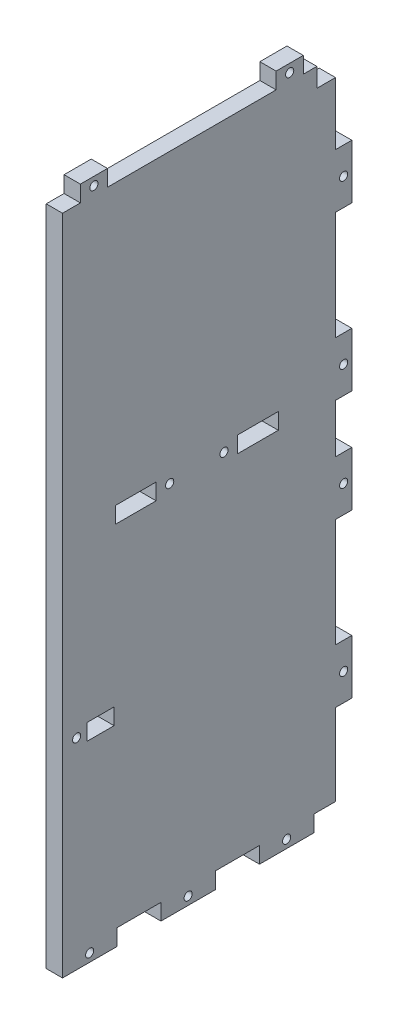
SolidWorks part; units mm, degrees
ref_plane "Plan de face" through (0, 0, 0) normal (0, 0, 1) x (1, 0, 0)
ref_plane "Plan de dessus" through (0, 0, 0) normal (0, 1, 0) x (1, 0, 0)
ref_plane "Plan de droite" through (0, 0, 0) normal (1, 0, 0) x (0, 0, -1)
sketch "Esquisse1" plane through (0, 0, 0) normal (1, 0, 0) x (0, 0, -1)
  line L0 (97.1531, 0) -> (-102.2664, 0) construction
  line L1 (-50.29, 119) -> (50.29, 119)
  line L2 (-50.29, 119) -> (-50.29, -119)
  line L3 (-50.29, -119) -> (50.29, -119)
  line L4 (50.29, 119) -> (50.29, -119)
  line L5 (0, 172.7153) -> (0, -236.1933) construction
  line L7 (-41.29, -48) -> (-31.29, -48)
  line L8 (-41.29, -48) -> (-41.29, -54)
  line L9 (-41.29, -54) -> (-31.29, -54)
  line L10 (-31.29, -48) -> (-31.29, -54)
  line L15 (-30.795, 16) -> (-15.795, 16)
  line L16 (-30.795, 16) -> (-30.795, 10)
  line L17 (-30.795, 10) -> (-15.795, 10)
  line L18 (-15.795, 16) -> (-15.795, 10)
  line L19 (14.205, 16) -> (29.205, 16)
  line L20 (14.205, 16) -> (14.205, 10)
  line L21 (14.205, 10) -> (29.205, 10)
  line L22 (29.205, 16) -> (29.205, 10)
  dimension "D1" = 238
  dimension "D2" = 100.58
  dimension "D4" = 119
  dimension "D13" = 15
  dimension "D14" = 15
  dimension "D15" = 30
  dimension "D16" = 6
  dimension "D17" = 6
  dimension "D3" = 50.29
  dimension "D5" = 103
  dimension "D6" = 19.495
  dimension "D7" = 9
  dimension "D8" = 167
  dimension "D9" = 6
  dimension "D10" = 10
extrude "Boss.-Extru.1" add sketch "Esquisse1" along normal blind 6
sketch "Esquisse3" plane through (6, 0, 0) normal (1, 0, 0) x (0, 0, -1)
  line L0 (-50.29, -119) -> (50.29, -119) construction
  line L1 (-50.29, -119) -> (-30.29, -119)
  line L2 (-50.29, -119) -> (-50.29, -125)
  line L3 (-50.29, -125) -> (-30.29, -125)
  line L4 (-30.29, -119) -> (-30.29, -125)
  line L5 (245.3741, 0) -> (-166.5298, 0) construction
  line L6 (50.29, -119) -> (50.29, 119) construction
  line L7 (22.29, -119) -> (42.29, -119)
  line L8 (22.29, -119) -> (22.29, -125)
  line L9 (22.29, -125) -> (42.29, -125)
  line L10 (0, 208.6671) -> (0, -232.3841) construction
  line L11 (-50.29, -119) -> (50.29, -119) construction
  line L12 (42.29, -119) -> (42.29, -125)
  line L13 (56.29, 29) -> (56.29, 9)
  line L14 (50.29, 9) -> (56.29, 9)
  line L15 (50.29, 29) -> (50.29, 9)
  line L16 (50.29, 29) -> (56.29, 29)
  line L17 (56.29, 89) -> (56.29, 69)
  line L18 (50.29, 69) -> (56.29, 69)
  line L19 (50.29, 89) -> (50.29, 69)
  line L20 (50.29, 89) -> (56.29, 89)
  line L21 (50.29, 119) -> (-50.29, 119) construction
  line L22 (50.29, -89) -> (56.29, -89)
  line L23 (50.29, -89) -> (50.29, -69)
  line L24 (50.29, -69) -> (56.29, -69)
  line L25 (56.29, -89) -> (56.29, -69)
  line L26 (50.29, -29) -> (56.29, -29)
  line L27 (50.29, -29) -> (50.29, -9)
  line L28 (50.29, -9) -> (56.29, -9)
  line L29 (0, -208.6671) -> (0, 232.3841) construction
  line L30 (-14, -119) -> (6, -119)
  line L31 (-14, -119) -> (-14, -125)
  line L32 (-14, -125) -> (6, -125)
  line L33 (6, -119) -> (6, -125)
  line L34 (50.29, -119) -> (50.29, 119) construction
  line L35 (56.29, -29) -> (56.29, -9)
  line L36 (38.41, 119) -> (28.41, 119)
  line L37 (38.41, 119) -> (38.41, 125)
  line L38 (38.41, 125) -> (28.41, 125)
  line L39 (28.41, 119) -> (28.41, 125)
  line L40 (-50.29, 119) -> (-50.29, -119) construction
  line L41 (-33.71, 119) -> (-43.71, 119)
  line L42 (-33.71, 119) -> (-33.71, 125)
  line L43 (-33.71, 125) -> (-43.71, 125)
  line L44 (-43.71, 119) -> (-43.71, 125)
  dimension "D2" = 20
  dimension "D3" = 6
  dimension "D4" = 20
  dimension "D5" = 8
  dimension "D6" = 6
  dimension "D7" = 6
  dimension "D8" = 20
  dimension "D9" = 6
  dimension "D10" = 20
  dimension "D11" = 6
  dimension "D12" = 20
  dimension "D13" = 16.29
  dimension "D14" = 30
  dimension "D15" = 40
  dimension "D16" = 6
  dimension "D17" = 10
  dimension "D18" = 11.88
  dimension "D19" = 6.58
  dimension "D20" = 10
  dimension "D21" = 6
  dimension "D22" = 16.29
extrude "Boss.-Extru.5" add sketch "Esquisse3" against normal blind 6
sketch "Esquisse7" plane through (0, 0, 0) normal (-1, 0, 0) x (0, 0, 1)
  line L1 (-50.29, 119) -> (-43.41, 119)
  line L2 (-50.29, 119) -> (-50.29, 112)
  line L3 (-50.29, 112) -> (-43.41, 112)
  line L4 (-43.41, 119) -> (-43.41, 112)
  dimension "D1" = 7
  dimension "D2" = 6.88
extrude "Enlèv. mat.-Extru.3" cut sketch "Esquisse7" against normal blind 6
sketch "Esquisse8" plane through (0, 0, 0) normal (-1, 0, 0) x (0, 0, 1)
  line L0 (-51.0214, 13) -> (44.3386, 13) construction
  line L1 (50.29, -125) -> (30.29, -125) construction
  line L2 (-14.205, 16) -> (-14.205, 10) construction
  line L3 (15.795, 10) -> (15.795, 16) construction
  line L4 (14, -119) -> (14, -125) construction
  line L5 (60.5401, -51) -> (10.4957, -51) construction
  line L6 (41.29, -48) -> (41.29, -54) construction
  line L8 (41.29, -54) -> (31.29, -54) construction
  line L9 (53.2872, 122) -> (-67.0711, 122) construction
  line L10 (33.71, 125) -> (43.71, 125) construction
  line L11 (-28.41, 125) -> (-28.41, 119) construction
  line L12 (33.71, 119) -> (33.71, 125) construction
  line L13 (-67.0711, -122) -> (72.8873, -122) construction
  line L14 (15.795, 16) -> (30.795, 16) construction
  line L16 (-22.29, -119) -> (-22.29, -125) construction
  line L17 (30.29, -125) -> (30.29, -119) construction
  line L18 (-53.29, 135.0788) -> (-53.29, -173.0788) construction
  line L19 (-56.29, 69) -> (-56.29, 89) construction
  line L21 (-56.29, -69) -> (-50.29, -69) construction
  line L22 (-50.29, 9) -> (-56.29, 9) construction
  line L23 (-56.29, 89) -> (-50.29, 89) construction
  circle A0 centre (4, -122) radius 1.5
  circle A1 centre (-9.205, 13) radius 1.5
  circle A2 centre (10.795, 13) radius 1.5
  circle A5 centre (45.08, -51) radius 1.5
  circle A6 centre (38.71, 122) radius 1.5
  circle A7 centre (-33.41, 122) radius 1.5
  circle A8 centre (40.29, -122) radius 1.5
  circle A9 centre (-53.29, 79) radius 1.5
  circle A10 centre (-32.29, -122) radius 1.5
  circle A11 centre (-53.29, 19) radius 1.5
  circle A12 centre (-53.29, -79) radius 1.5
  circle A13 centre (-53.29, -19) radius 1.5
  dimension "D1" = 3
  dimension "D2" = 3
  dimension "D4" = 3
  dimension "D5" = 3
  dimension "D6" = 5
  dimension "D7" = 5
  dimension "D8" = 10
  dimension "D10" = 3
  dimension "D15" = 3
  dimension "D16" = 3
  dimension "D17" = 5
  dimension "D18" = 5
  dimension "D20" = 3
  dimension "D21" = 3
  dimension "D22" = 3
  dimension "D23" = 3
  dimension "D24" = 10
  dimension "D25" = 10
  dimension "D26" = 3
  dimension "D27" = 3
  dimension "D28" = 3
  dimension "D29" = 10
  dimension "D31" = 10
  dimension "D32" = 10
  dimension "D11" = 3.79
  dimension "D13" = 3
  dimension "D14" = 3
  dimension "D19" = 3
  dimension "D30" = 10
extrude "Enlèv. mat.-Extru.4" cut sketch "Esquisse8" against normal blind 6
equation "\"D3@Esquisse1\"=\"D2@Esquisse1\"/2"
equation "\"D4@Esquisse1\"=\"D1@Esquisse1\"/2"
